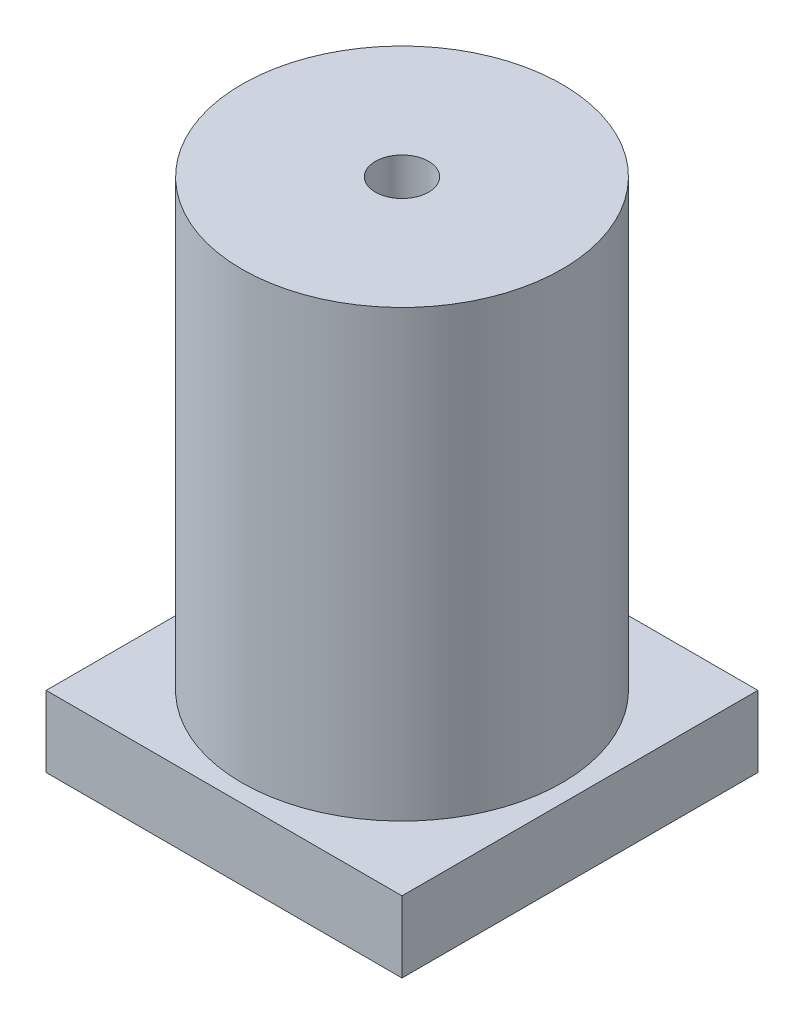
SolidWorks part; units mm, degrees
ref_plane "Plano frontal" through (0, 0, 0) normal (0, 0, 1) x (1, 0, 0)
ref_plane "Plano superior" through (0, 0, 0) normal (0, 1, 0) x (1, 0, 0)
ref_plane "Plano direito" through (0, 0, 0) normal (1, 0, 0) x (0, 0, -1)
sketch "Esboço2" plane through (0, 0, 0) normal (0, 1, 0) x (1, 0, 0)
  line L1 (-100, -100) -> (100, -100)
  line L2 (-100, -100) -> (-100, 100)
  line L3 (-100, 100) -> (100, 100)
  line L4 (100, -100) -> (100, 100)
  line L5 (-100, -100) -> (100, 100) construction
  line L6 (-100, 100) -> (100, -100) construction
  point P0 (0, 0)
  dimension "D1" = 200
  dimension "D2" = 200
extrude "Ressalto-extrusão1" add sketch "Esboço2" along normal blind 40
sketch "Esboço3" plane through (0, 40, 0) normal (0, 1, 0) x (1, 0, 0)
  circle A0 centre (0, 0) radius 90
  dimension "D1" = 180
extrude "Ressalto-extrusão2" add sketch "Esboço3" along normal blind 250
sketch "Esboço4" plane through (0, 290, 0) normal (0, 1, 0) x (1, 0, 0)
  circle A0 centre (0, 0) radius 15
  dimension "D1" = 30
extrude "Corte-extrusão1" cut sketch "Esboço4" against normal blind 25
